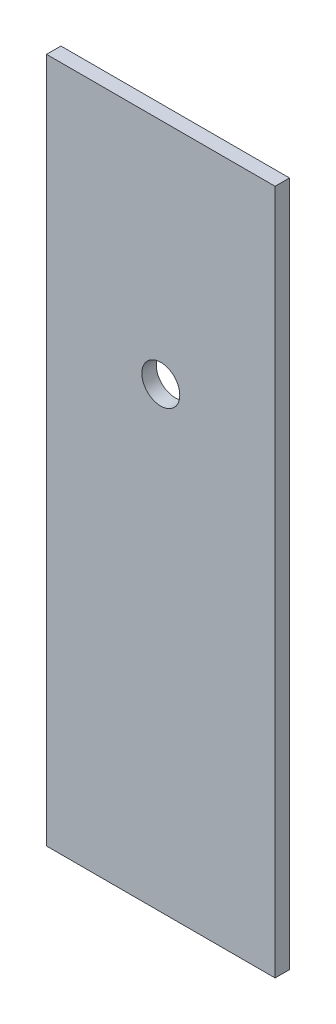
SolidWorks part; units mm, degrees
ref_plane "Front Plane" through (0, 0, 0) normal (0, 0, 1) x (1, 0, 0)
ref_plane "Top Plane" through (0, 0, 0) normal (0, 1, 0) x (1, 0, 0)
ref_plane "Right Plane" through (0, 0, 0) normal (1, 0, 0) x (0, 0, -1)
sketch "Sketch1" plane through (0, 0, 0) normal (0, 0, 1) x (1, 0, 0)
  line L1 (-12.7, 38.1) -> (12.7, 38.1)
  line L2 (-12.7, 38.1) -> (-12.7, -38.1)
  line L3 (-12.7, -38.1) -> (12.7, -38.1)
  line L4 (12.7, 38.1) -> (12.7, -38.1)
  line L5 (-12.7, 38.1) -> (12.7, -38.1) construction
  line L6 (-12.7, -38.1) -> (12.7, 38.1) construction
  point P0 (0, 0)
  dimension "D1" = 25.4
  dimension "D2" = 76.2
extrude "Boss-Extrude1" add sketch "Sketch1" along normal blind 1.6002
sketch "Sketch2" plane through (0, 0, 1.6002) normal (0, 0, 1) x (1, 0, 0)
  line L0 (12.7, 38.1) -> (-12.7, 38.1) construction
  circle A0 centre (0, 12.7) radius 2.1082
  dimension "D2" = 4.2164
  dimension "D1" = 25.4
extrude "Cut-Extrude1" cut sketch "Sketch2" against normal blind 1.6002
